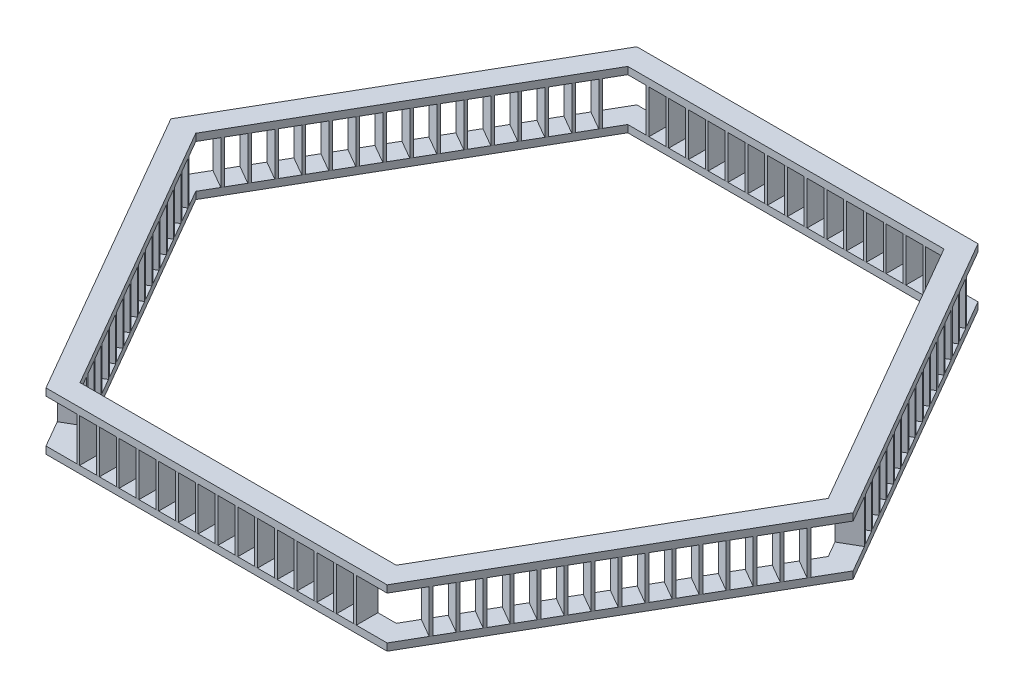
SolidWorks part; units mm, degrees
ref_plane "前视基准面" through (0, 0, 0) normal (0, 0, 1) x (1, 0, 0)
ref_plane "上视基准面" through (0, 0, 0) normal (0, 1, 0) x (1, 0, 0)
ref_plane "右视基准面" through (0, 0, 0) normal (1, 0, 0) x (0, 0, -1)
sketch "草图1" plane through (0, 0, 0) normal (0, 1, 0) x (1, 0, 0)
  line L0 (-1186.6025, -2055.2559) -> (1186.6025, -2055.2559)
  line L1 (-1100, -1905.2559) -> (1100, -1905.2559)
  line L2 (1100, -1905.2559) -> (2200, 0)
  line L3 (2200, 0) -> (1100, 1905.2559)
  line L4 (1100, 1905.2559) -> (-1100, 1905.2559)
  line L5 (-1100, 1905.2559) -> (-2200, 0)
  line L6 (-2200, 0) -> (-1100, -1905.2559)
  line L7 (1186.6025, -2055.2559) -> (2373.2051, 0)
  line L8 (2373.2051, 0) -> (1186.6025, 2055.2559)
  line L9 (1186.6025, 2055.2559) -> (-1186.6025, 2055.2559)
  line L10 (-1186.6025, 2055.2559) -> (-2373.2051, 0)
  line L11 (-2373.2051, 0) -> (-1186.6025, -2055.2559)
  circle A0 centre (0, 0) radius 1905.2559 construction
  dimension "D1" = 2200
  dimension "D2" = 150
extrude "凸台-拉伸2" add sketch "草图1" along normal blind 50
ref_plane "基准面2" through (0, 50, 0) normal (0, 1, 0) x (1, 0, 0)
sketch "草图2" plane through (0, 50, 0) normal (0, 1, 0) x (1, 0, 0)
  line L0 (0, 1905.2559) -> (0, 2055.2559) construction
  line L1 (1100, 1905.2559) -> (-1100, 1905.2559) construction
  line L2 (1186.6025, 2055.2559) -> (-1186.6025, 2055.2559) construction
  line L3 (-1100, 1905.2559) -> (-1100, 2055.2559) construction
  line L4 (1100, 1905.2559) -> (1100, 2055.2559) construction
  line L5 (0, 1905.2559) -> (-1100, 1905.2559) construction
  line L6 (-550, 1905.2559) -> (-550, 2055.2559) construction
  line L7 (-550, 2055.2559) -> (0, 2055.2559) construction
  line L8 (0, 1905.2559) -> (1100, 1905.2559) construction
  line L9 (550, 1905.2559) -> (550, 2055.2559) construction
  line L10 (0, 2055.2559) -> (550, 2055.2559) construction
  line L11 (550, 2055.2559) -> (1100, 2055.2559) construction
  line L12 (275, 2055.2559) -> (275, 1905.2559) construction
  line L13 (825, 2055.2559) -> (825, 1905.2559) construction
  line L14 (0, 2055.2559) -> (-550, 2055.2559) construction
  line L15 (-550, 2055.2559) -> (-1100, 2055.2559) construction
  line L16 (-825, 2055.2559) -> (-825, 1905.2559) construction
  line L17 (-275, 2055.2559) -> (-275, 1905.2559) construction
  line L18 (275, 2055.2559) -> (0, 2055.2559) construction
  line L19 (137.5, 2055.2559) -> (137.5, 1905.2559) construction
  line L20 (275, 2055.2559) -> (550, 2055.2559) construction
  line L21 (550, 2055.2559) -> (825, 2055.2559) construction
  line L22 (825, 2055.2559) -> (1100, 2055.2559) construction
  line L23 (412.5, 2055.2559) -> (412.5, 1905.2559) construction
  line L24 (687.5, 2055.2559) -> (687.5, 1905.2559) construction
  line L25 (962.5, 2055.2559) -> (962.5, 1905.2559) construction
  line L26 (0, 2055.2559) -> (-275, 2055.2559) construction
  line L27 (-275, 2055.2559) -> (-550, 2055.2559) construction
  line L28 (-550, 2055.2559) -> (-825, 2055.2559) construction
  line L29 (-825, 2055.2559) -> (-1100, 2055.2559) construction
  line L30 (-962.5, 2055.2559) -> (-962.5, 1905.2559) construction
  line L31 (-687.5, 2055.2559) -> (-687.5, 1905.2559) construction
  line L32 (-412.5, 2055.2559) -> (-412.5, 1905.2559) construction
  line L33 (-137.5, 2055.2559) -> (-137.5, 1905.2559) construction
  line L34 (127.5, 1905.2559) -> (127.5, 2055.2559)
  line L35 (127.5, 1905.2559) -> (147.5, 1905.2559)
  line L36 (127.5, 2055.2559) -> (147.5, 2055.2559)
  line L37 (147.5, 1905.2559) -> (147.5, 2055.2559)
  line L38 (127.5, 1905.2559) -> (147.5, 2055.2559) construction
  line L39 (127.5, 2055.2559) -> (147.5, 1905.2559) construction
  line L40 (422.5, 2055.2559) -> (402.5, 1905.2559) construction
  line L41 (422.5, 1905.2559) -> (402.5, 2055.2559) construction
  line L42 (422.5, 1905.2559) -> (402.5, 1905.2559)
  line L43 (422.5, 1905.2559) -> (422.5, 2055.2559)
  line L44 (422.5, 2055.2559) -> (402.5, 2055.2559)
  line L45 (402.5, 1905.2559) -> (402.5, 2055.2559)
  line L46 (677.5, 1905.2559) -> (697.5, 1905.2559)
  line L47 (677.5, 1905.2559) -> (697.5, 2055.2559) construction
  line L48 (677.5, 2055.2559) -> (697.5, 1905.2559) construction
  line L49 (677.5, 1905.2559) -> (677.5, 2055.2559)
  line L50 (697.5, 1905.2559) -> (697.5, 2055.2559)
  line L51 (677.5, 2055.2559) -> (697.5, 2055.2559)
  line L52 (972.5, 1905.2559) -> (952.5, 2055.2559) construction
  line L53 (972.5, 2055.2559) -> (952.5, 1905.2559) construction
  line L54 (972.5, 1905.2559) -> (952.5, 1905.2559)
  line L55 (972.5, 1905.2559) -> (972.5, 2055.2559)
  line L56 (972.5, 2055.2559) -> (952.5, 2055.2559)
  line L57 (952.5, 1905.2559) -> (952.5, 2055.2559)
  line L58 (-422.5, 1905.2559) -> (-422.5, 2055.2559)
  line L59 (-972.5, 2055.2559) -> (-952.5, 2055.2559)
  line L60 (-972.5, 1905.2559) -> (-952.5, 1905.2559)
  line L61 (-952.5, 1905.2559) -> (-952.5, 2055.2559)
  line L62 (-972.5, 1905.2559) -> (-972.5, 2055.2559)
  line L63 (-677.5, 1905.2559) -> (-697.5, 1905.2559)
  line L64 (-697.5, 1905.2559) -> (-697.5, 2055.2559)
  line L65 (-677.5, 2055.2559) -> (-697.5, 2055.2559)
  line L66 (-677.5, 1905.2559) -> (-677.5, 2055.2559)
  line L67 (-422.5, 1905.2559) -> (-402.5, 1905.2559)
  line L68 (-422.5, 2055.2559) -> (-402.5, 2055.2559)
  line L69 (-402.5, 1905.2559) -> (-402.5, 2055.2559)
  line L70 (-127.5, 1905.2559) -> (-147.5, 1905.2559)
  line L71 (-127.5, 1905.2559) -> (-127.5, 2055.2559)
  line L72 (-127.5, 2055.2559) -> (-147.5, 2055.2559)
  line L73 (-147.5, 1905.2559) -> (-147.5, 2055.2559)
  line L74 (962.5, 1905.2559) -> (825, 1905.2559) construction
  line L75 (893.75, 1905.2559) -> (893.75, 2055.2559) construction
  line L76 (815, 2055.2559) -> (835, 2055.2559)
  line L77 (815, 1905.2559) -> (835, 1905.2559)
  line L78 (815, 1905.2559) -> (815, 2055.2559)
  line L79 (815, 1905.2559) -> (835, 2055.2559) construction
  line L80 (815, 2055.2559) -> (835, 1905.2559) construction
  line L81 (835, 1905.2559) -> (835, 2055.2559)
  line L82 (285, 2055.2559) -> (265, 2055.2559)
  line L83 (285, 2055.2559) -> (265, 1905.2559) construction
  line L84 (285, 1905.2559) -> (265, 2055.2559) construction
  line L85 (285, 1905.2559) -> (285, 2055.2559)
  line L86 (265, 1905.2559) -> (265, 2055.2559)
  line L87 (285, 1905.2559) -> (265, 1905.2559)
  line L88 (560, 1905.2559) -> (540, 2055.2559) construction
  line L89 (560, 2055.2559) -> (540, 1905.2559) construction
  line L90 (560, 2055.2559) -> (540, 2055.2559)
  line L91 (560, 1905.2559) -> (540, 1905.2559)
  line L92 (540, 1905.2559) -> (540, 2055.2559)
  line L93 (560, 1905.2559) -> (560, 2055.2559)
  line L94 (-10, 1905.2559) -> (10, 1905.2559)
  line L95 (-10, 1905.2559) -> (-10, 2055.2559)
  line L96 (-10, 2055.2559) -> (10, 2055.2559)
  line L97 (-10, 2055.2559) -> (10, 1905.2559) construction
  line L98 (-10, 1905.2559) -> (10, 2055.2559) construction
  line L99 (10, 1905.2559) -> (10, 2055.2559)
  line L100 (-265, 2055.2559) -> (-285, 2055.2559)
  line L101 (-265, 1905.2559) -> (-285, 1905.2559)
  line L102 (-285, 1905.2559) -> (-285, 2055.2559)
  line L103 (-265, 1905.2559) -> (-265, 2055.2559)
  line L104 (-540, 1905.2559) -> (-560, 2055.2559) construction
  line L105 (-540, 2055.2559) -> (-560, 1905.2559) construction
  line L106 (-540, 2055.2559) -> (-560, 2055.2559)
  line L107 (-540, 1905.2559) -> (-540, 2055.2559)
  line L108 (-540, 1905.2559) -> (-560, 1905.2559)
  line L109 (-560, 1905.2559) -> (-560, 2055.2559)
  line L110 (-835, 2055.2559) -> (-815, 2055.2559)
  line L111 (-835, 2055.2559) -> (-815, 1905.2559) construction
  line L112 (-835, 1905.2559) -> (-815, 2055.2559) construction
  line L113 (-835, 1905.2559) -> (-835, 2055.2559)
  line L114 (-815, 1905.2559) -> (-815, 2055.2559)
  line L115 (-835, 1905.2559) -> (-815, 1905.2559)
  point P41 (137.5, 1980.2559)
  point P47 (137.5, 1980.2559)
  dimension "D1" = 20
extrude "凸台-拉伸3" add sketch "草图2" along normal blind 300 separate body
sketch "草图3" plane through (0, 0, 0) normal (0, 0, 1) x (1, 0, 0)
  line L0 (0, 0) -> (0, 600) construction
  dimension "D1" = 600
pattern_circular "阵列(圆周)2" count 6 every 60 about axis through (0, 0, 0) along (0, 1, 0)
ref_plane "基准面3" through (0, 350, 0) normal (0, 1, 0) x (1, 0, 0)
sketch "草图5" plane through (0, 350, 0) normal (0, 1, 0) x (1, 0, 0)
  line L0 (-2373.2051, 0) -> (-1186.6025, -2055.2559) construction
  line L1 (-2200, 0) -> (-1100, -1905.2559) construction
  line L2 (-1186.6025, -2055.2559) -> (1186.6025, -2055.2559) construction
  line L3 (-1100, -1905.2559) -> (1100, -1905.2559) construction
  line L4 (1100, -1905.2559) -> (2200, 0) construction
  line L5 (1186.6025, -2055.2559) -> (2373.2051, 0) construction
  line L6 (2373.2051, 0) -> (1186.6025, 2055.2559) construction
  line L7 (2200, 0) -> (1100, 1905.2559) construction
  line L8 (1100, 1905.2559) -> (-1100, 1905.2559) construction
  line L9 (1186.6025, 2055.2559) -> (-1186.6025, 2055.2559) construction
  line L10 (-1186.6025, 2055.2559) -> (-2373.2051, 0) construction
  line L11 (-1100, 1905.2559) -> (-2200, 0) construction
  line L12 (-2373.2051, 0) -> (-1186.6025, -2055.2559)
  line L13 (-2200, 0) -> (-1100, -1905.2559)
  line L14 (-1186.6025, -2055.2559) -> (1186.6025, -2055.2559)
  line L15 (-1100, -1905.2559) -> (1100, -1905.2559)
  line L16 (1100, -1905.2559) -> (2200, 0)
  line L17 (1186.6025, -2055.2559) -> (2373.2051, 0)
  line L18 (2373.2051, 0) -> (1186.6025, 2055.2559)
  line L19 (2200, 0) -> (1100, 1905.2559)
  line L20 (1100, 1905.2559) -> (-1100, 1905.2559)
  line L21 (1186.6025, 2055.2559) -> (-1186.6025, 2055.2559)
  line L22 (-1186.6025, 2055.2559) -> (-2373.2051, 0)
  line L23 (-1100, 1905.2559) -> (-2200, 0)
extrude "凸台-拉伸5" add sketch "草图5" along normal blind 50
